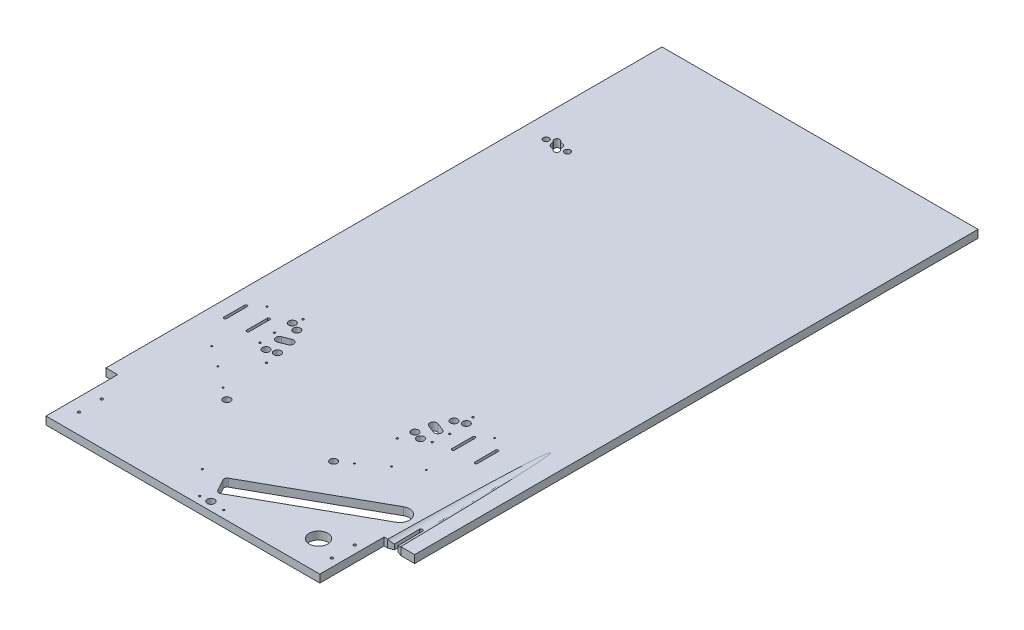
SolidWorks part; units mm, degrees
ref_plane "Front Plane" through (0, 0, 0) normal (0, 0, 1) x (1, 0, 0)
ref_plane "Top Plane" through (0, 0, 0) normal (0, 1, 0) x (1, 0, 0)
ref_plane "Right Plane" through (0, 0, 0) normal (1, 0, 0) x (0, 0, -1)
sketch "Sketch1" plane through (0, 0, 0) normal (0, 1, 0) x (1, 0, 0)
  line L0 (181.0536, 279.5919) -> (200.0932, 279.5919)
  line L1 (200.0932, 279.5919) -> (200.0932, 162.9446)
  line L2 (200.0932, 162.9446) -> (645.715, 162.9446)
  line L3 (645.715, 162.9446) -> (645.715, 267.5416)
  line L4 (695.3624, 267.5416) -> (695.3624, 1184.4278)
  line L5 (181.0536, 279.5919) -> (181.0536, 1184.4278)
  line L6 (695.3624, 1184.4278) -> (181.0536, 1184.4278)
  line L7 (673.2538, 267.5416) -> (695.3624, 267.5416)
  line L8 (645.715, 267.5416) -> (651.4598, 267.5416)
  line L9 (659.5927, 310.9274) -> (659.5927, 270.5881)
  line L10 (665.1208, 310.9274) -> (665.1208, 270.5881)
  line L11 (659.5927, 270.5881) -> (651.4598, 267.5416)
  line L12 (665.1208, 270.5881) -> (673.2538, 267.5416)
  line L13 (280.0435, 466.342) -> (292.2844, 471.0804)
  line L14 (284.2486, 455.479) -> (296.4894, 460.2174)
  line L15 (542.1235, 466.342) -> (529.8827, 471.0804)
  line L16 (537.9184, 455.479) -> (525.6776, 460.2174)
  line L17 (651.4598, 267.5416) -> (658.0675, 570.4425) construction
  line L18 (673.2538, 267.5416) -> (666.646, 570.4425) construction
  line L19 (209.7077, 480.9937) -> (209.7077, 447.1932)
  line L20 (205.4432, 480.9937) -> (205.4432, 447.1932)
  line L21 (242.2446, 480.9937) -> (242.2446, 447.1932)
  line L22 (246.5092, 480.9937) -> (246.5092, 447.1932)
  line L23 (576.3522, 480.9937) -> (576.3522, 447.1932)
  line L24 (580.6168, 480.9937) -> (580.6168, 447.1932)
  line L25 (613.8645, 480.9937) -> (613.8645, 447.1932)
  line L26 (618.129, 480.9937) -> (618.129, 447.1932)
  line L27 (640.6198, 319.7104) -> (640.545, 319.8441)
  line L28 (444.7655, 197.855) -> (434.1549, 216.8357)
  line L29 (451.7614, 195.8762) -> (634.4854, 298.0231)
  line L30 (436.1337, 223.8316) -> (618.8577, 325.9785)
  line L31 (235.7134, 952.3283) -> (237.8585, 950.0949)
  line L32 (241.9789, 958.3457) -> (244.1239, 956.1123)
  line L33 (224.9266, 963.5598) -> (227.0716, 961.3264)
  line L34 (231.192, 969.5772) -> (233.3371, 967.3438)
  arc A0 (665.1208, 310.9274) -> (659.5927, 310.9274) centre (662.3568, 310.9274) ccw
  circle A1 centre (324.1637, 333.1564) radius 5.8243
  circle A2 centre (498.0033, 333.1564) radius 5.8243
  circle A3 centre (285.4549, 435.7267) radius 5.8243
  circle A4 centre (269.4783, 494.3735) radius 5.8243
  circle A5 centre (283.1135, 488.0773) radius 5.8243
  circle A6 centre (299.2832, 440.4565) radius 5.8243
  arc A7 (280.0435, 466.342) -> (284.2486, 455.479) centre (282.1461, 460.9105) ccw
  arc A8 (296.4894, 460.2174) -> (292.2844, 471.0804) centre (294.3869, 465.6489) ccw
  circle A9 centre (536.7121, 435.7267) radius 5.8243
  circle A10 centre (552.6888, 494.3735) radius 5.8243
  circle A11 centre (539.0535, 488.0773) radius 5.8243
  circle A12 centre (522.8838, 440.4565) radius 5.8243
  arc A13 (537.9184, 455.479) -> (542.1235, 466.342) centre (540.021, 460.9105) ccw
  arc A14 (529.8827, 471.0804) -> (525.6776, 460.2174) centre (527.7801, 465.6489) ccw
  arc A15 (666.646, 570.4425) -> (662.3568, 670.5528) centre (-40289.7772, -1134.2001) ccw construction
  arc A16 (662.3568, 670.5528) -> (658.0675, 570.4425) centre (41614.4907, -1134.2001) ccw construction
  arc A17 (242.2446, 447.1932) -> (246.5092, 447.1932) centre (244.3769, 447.1932) ccw
  arc A18 (209.7077, 480.9937) -> (205.4432, 480.9937) centre (207.5754, 480.9937) ccw
  arc A19 (205.4432, 447.1932) -> (209.7077, 447.1932) centre (207.5754, 447.1932) ccw
  arc A20 (246.5092, 480.9937) -> (242.2446, 480.9937) centre (244.3769, 480.9937) ccw
  arc A21 (576.3522, 447.1932) -> (580.6168, 447.1932) centre (578.4845, 447.1932) ccw
  arc A22 (580.6168, 480.9937) -> (576.3522, 480.9937) centre (578.4845, 480.9937) ccw
  arc A23 (613.8645, 447.1932) -> (618.129, 447.1932) centre (615.9967, 447.1932) ccw
  arc A24 (618.129, 480.9937) -> (613.8645, 480.9937) centre (615.9967, 480.9937) ccw
  circle A25 centre (594.651, 211.8803) radius 15.1834
  circle A26 centre (221.6125, 232.3839) radius 2.0977
  circle A27 centre (221.6125, 195.2418) radius 2.0977
  circle A28 centre (633.0691, 232.3839) radius 2.0977
  circle A29 centre (633.0691, 195.2418) radius 2.0977
  arc A30 (640.545, 319.8441) -> (618.8577, 325.9785) centre (626.6342, 312.0677) ccw
  arc A31 (634.4854, 298.0231) -> (640.6198, 319.7104) centre (626.709, 311.9339) ccw
  arc A32 (444.7655, 197.855) -> (451.7614, 195.8762) centre (449.2529, 200.3636) ccw
  arc A33 (436.1337, 223.8316) -> (434.1549, 216.8357) centre (438.6422, 219.3442) ccw
  circle A34 centre (402.1965, 215.3626) radius 1.5012
  circle A35 centre (438.228, 175.1357) radius 1.5012
  circle A36 centre (477.221, 175.1357) radius 1.5012
  circle A37 centre (454.6396, 176.8632) radius 6.0464
  circle A38 centre (225.8321, 496.8949) radius 1.234
  circle A39 centre (236.5676, 396.2967) radius 1.234
  circle A40 centre (269.8844, 372.8515) radius 1.234
  circle A41 centre (304.2809, 346.9385) radius 1.234
  circle A42 centre (596.3349, 496.8949) radius 1.234
  circle A43 centre (585.5995, 396.2967) radius 1.234
  circle A44 centre (552.2827, 372.8515) radius 1.234
  circle A45 centre (517.8862, 346.9385) radius 1.234
  circle A46 centre (217.2005, 959.836) radius 4.7384
  circle A47 centre (251.85, 959.836) radius 4.7384
  arc A48 (231.192, 969.5772) -> (224.9266, 963.5598) centre (228.0593, 966.5685) ccw
  arc A49 (241.9789, 958.3457) -> (233.3371, 967.3438) centre (234.5253, 959.836) ccw
  arc A50 (237.8585, 950.0949) -> (244.1239, 956.1123) centre (240.9912, 953.1036) ccw
  arc A51 (227.0716, 961.3264) -> (235.7134, 952.3283) centre (234.5253, 959.836) ccw
  circle A52 centre (272.8947, 508.6431) radius 1.524
  circle A53 centre (268.4506, 466.3964) radius 1.524
  circle A54 centre (271.1266, 440.4086) radius 1.524
  circle A55 centre (304.4733, 417.2923) radius 1.524
  circle A56 centre (549.2723, 508.6431) radius 1.524
  circle A57 centre (553.7164, 466.3964) radius 1.524
  circle A58 centre (551.0405, 440.4086) radius 1.524
  circle A59 centre (517.6937, 417.2923) radius 1.524
extrude "Boss-Extrude1" add sketch "Sketch1" along normal blind 12.7
ref_plane "Plane2" through (662.3568, 0, 0) normal (1, 0, 0) x (0, 0, -1)
sketch "Sketch2" plane through (662.3568, 0, 0) normal (1, 0, 0) x (0, 0, -1)
  line L0 (267.5416, 12.7) -> (267.5416, 0) construction
  line L1 (267.5416, 12.7) -> (267.5416, 0) construction
  line L2 (267.5416, 12.7) -> (521.5416, 17.4625)
  line L3 (267.5416, 12.7) -> (1184.4278, 12.7) construction
  line L4 (267.5416, 12.7) -> (1184.4278, 12.7) construction
  dimension "D1" = 254
  dimension "D2" = 4.7625
sketch "Sketch3" plane through (0, 0, -267.5416) normal (0, 0, 1) x (1, 0, 0)
  line L0 (662.3568, 6.9261) -> (662.3568, 54.1093) construction
  line L1 (662.3568, -9.6044) -> (662.3568, 9.6044) construction
  line L2 (673.2538, 12.7) -> (695.3624, 12.7) construction
  circle A0 centre (662.3568, 22.225) radius 14.2875
  dimension "D1" = 28.575
  dimension "D2" = 9.525
sweep "Cut-Sweep1" cut profiles "Sketch3" path "Sketch2"
